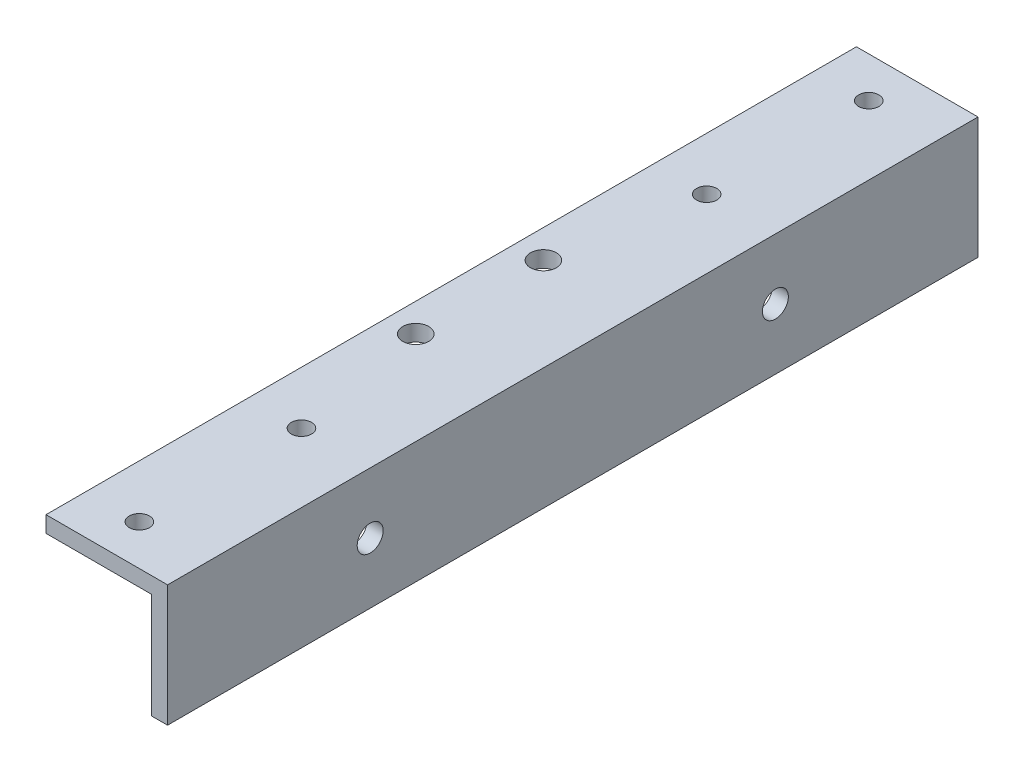
SolidWorks part; units mm, degrees
ref_plane "正面" through (0, 0, 0) normal (0, 0, 1) x (1, 0, 0)
ref_plane "平面" through (0, 0, 0) normal (0, 1, 0) x (1, 0, 0)
ref_plane "右側面" through (0, 0, 0) normal (1, 0, 0) x (0, 0, -1)
sketch "ｽｹｯﾁ1" plane through (0, 0, 0) normal (0, 0, 1) x (1, 0, 0)
  line L0 (0, 0) -> (15, 0)
  line L1 (15, 0) -> (15, -15)
  line L2 (15, -15) -> (13, -15)
  line L3 (13, -15) -> (13, -2)
  line L4 (13, -2) -> (0, -2)
  line L5 (0, -2) -> (0, 0)
  dimension "D1" = 2
  dimension "D2" = 2
  dimension "D3" = 15
  dimension "D4" = 15
extrude "ﾎﾞｽ - 押し出し1" add sketch "ｽｹｯﾁ1" along normal blind 100
sketch "ｽｹｯﾁ2" plane through (15, 0, 0) normal (1, 0, 0) x (0, 0, -1)
  line L0 (-50, 0) -> (-50, -7.5)
  line L1 (-100, 0) -> (0, 0) construction
  line L2 (-50, -7.5) -> (-25, -7.5)
  line L3 (-50, -7.5) -> (-75, -7.5)
  circle A0 centre (-75, -7.5) radius 1.6
  circle A1 centre (-25, -7.5) radius 1.6
  dimension "D4" = 3.2
  dimension "D5" = 3.2
  dimension "D1" = 7.5
  dimension "D2" = 25
  dimension "D3" = 25
sketch "ｽｹｯﾁ3" plane through (0, 0, 0) normal (0, 1, 0) x (1, 0, 0)
  line L0 (15, -50) -> (6.52, -50)
  line L1 (15, -100) -> (15, 0) construction
  line L2 (6.52, -50) -> (6.52, -75)
  line L3 (6.52, -50) -> (6.52, -25)
  line L4 (6.52, -75) -> (6.52, -95)
  line L5 (6.52, -95) -> (6.52, -100)
  line L6 (15, -100) -> (0, -100) construction
  line L7 (6.52, -25) -> (6.52, -5)
  line L8 (6.52, -5) -> (6.52, 0)
  line L9 (15, 0) -> (0, 0) construction
  circle A0 centre (6.52, -75) radius 1.6
  circle A1 centre (6.52, -25) radius 1.6
  circle A2 centre (6.52, -5) radius 1.2782
  circle A3 centre (6.52, -95) radius 2.1072
  dimension "D2" = 3.2
  dimension "D4" = 3.2
  dimension "D1" = 5
  dimension "D3" = 20
  dimension "D5" = 8.48
  dimension "D6" = 5
  dimension "D7" = 20
sketch "ｽｹｯﾁ4" plane through (0, 0, 0) normal (0, 1, 0) x (1, 0, 0)
  line L0 (3.5, -50) -> (3.5, -57.875)
  line L1 (3.5, -50) -> (0, -50)
  line L2 (0, -100) -> (0, 0) construction
  line L3 (3.5, -50) -> (3.5, -42.125)
  circle A0 centre (3.5, -57.875) radius 1.6
  circle A1 centre (3.5, -42.125) radius 1.6
  dimension "D4" = 3.2
  dimension "D5" = 3.2
  dimension "D1" = 3.5
  dimension "D2" = 7.875
  dimension "D3" = 7.875
extrude "ｶｯﾄ - 押し出し3" cut sketch "ｽｹｯﾁ4" against normal blind 2
hole_wizard "M3x0.5 ねじ穴1" positions "3Dｽｹｯﾁ2" profile "ｽｹｯﾁ6" tap size "M3x0.5" standard "JIS"
sketch3d "3Dｽｹｯﾁ2"
  point P0 (6.52, 0, 75)
  point P3 (6.52, 0, 25)
  point P6 (6.52, 0, 95)
  point P9 (6.52, 0, 5)
sketch "ｽｹｯﾁ6" plane through (6.52, 0, 75) normal (1, 0, 0) x (0, 0, 1)
  line L0 (0, 0) -> (0, 9.2511)
  line L1 (0, 9.2511) -> (1.25, 8.5)
  line L2 (1.25, 8.5) -> (1.25, 0)
  line L5 (1.25, 0) -> (0, 0)
  line L10 (0, 9.2511) -> (-1.25, 8.5) construction
  line L11 (0, -6.35) -> (0, 107.95) construction
  dimension "ねじ下穴ﾄﾞﾘﾙ直径" = 2.5
  dimension "ねじ下穴ﾄﾞﾘﾙの深さ" = 8.5
  dimension "ﾄﾞﾘﾙ角度" = 118
cosmetic thread "穴のねじ山1" parameters "D1"=2, "D2"=3
cosmetic thread "穴のねじ山2" parameters "D1"=2, "D2"=3
cosmetic thread "穴のねじ山3" parameters "D1"=2, "D2"=3
cosmetic thread "穴のねじ山4" parameters "D1"=2, "D2"=3
extrude "ｶｯﾄ - 押し出し4" cut sketch "ｽｹｯﾁ2" against normal blind 10
